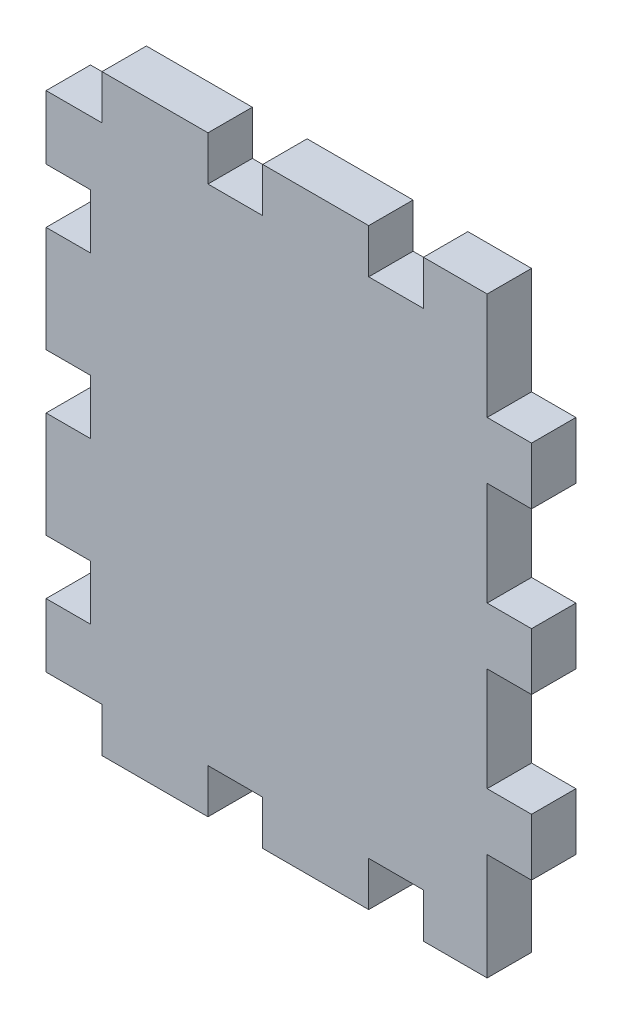
SolidWorks part; units mm, degrees
ref_plane "Front Plane" through (0, 0, 0) normal (0, 0, 1) x (1, 0, 0)
ref_plane "Top Plane" through (0, 0, 0) normal (0, 1, 0) x (1, 0, 0)
ref_plane "Right Plane" through (0, 0, 0) normal (1, 0, 0) x (0, 0, -1)
sketch "Sketch2" plane through (0, 0, 0) normal (0, 0, 1) x (1, 0, 0)
  line L1 (-2, 21.15) -> (-2, 17.975)
  line L2 (-13.5, 21.15) -> (-13.5, 17.975)
  line L3 (-13.5, 17.975) -> (-9.5, 17.975)
  line L4 (-9.5, 21.15) -> (-9.5, 17.975)
  line L5 (13.5, 21.15) -> (13.5, 17.975)
  line L6 (13.5, 17.975) -> (9.5, 17.975)
  line L9 (9.5, 21.15) -> (9.5, 17.975)
  line L10 (-2, 17.975) -> (2, 17.975)
  line L12 (-21.15, 21.15) -> (17.975, 21.15)
  line L13 (-21.15, 21.15) -> (-21.15, -21.15)
  line L14 (-21.15, -21.15) -> (17.975, -21.15)
  line L15 (21.15, 13.5) -> (21.15, 9.5)
  line L16 (-21.15, 21.15) -> (21.15, -21.15) construction
  line L17 (-21.15, -21.15) -> (21.15, 21.15) construction
  line L19 (17.975, 21.15) -> (17.975, 13.5)
  line L20 (21.15, 2) -> (21.15, -2)
  line L21 (21.15, -9.5) -> (21.15, -13.5)
  line L22 (17.975, 9.5) -> (17.975, 2)
  line L23 (17.975, -2) -> (17.975, -9.5)
  line L24 (17.975, -13.5) -> (17.975, -21.15)
  line L30 (2, 21.15) -> (2, 17.975)
  line L31 (-2, 21.15) -> (2, 17.975) construction
  line L32 (-2, 17.975) -> (2, 21.15) construction
  line L33 (-2, 21.15) -> (2, 21.15)
  line L34 (-2, -17.975) -> (-2, -21.15)
  line L35 (-13.5, -17.975) -> (-13.5, -21.15)
  line L36 (-13.5, -21.15) -> (-9.5, -21.15)
  line L37 (-9.5, -17.975) -> (-9.5, -21.15)
  line L38 (13.5, -17.975) -> (13.5, -21.15)
  line L39 (13.5, -21.15) -> (9.5, -21.15)
  line L40 (9.5, -17.975) -> (9.5, -21.15)
  line L41 (-2, -21.15) -> (2, -21.15)
  line L42 (2, -17.975) -> (2, -21.15)
  line L43 (-2, -17.975) -> (2, -21.15) construction
  line L44 (-2, -21.15) -> (2, -17.975) construction
  line L45 (-2, -17.975) -> (2, -17.975)
  line L46 (9.5, -17.975) -> (13.5, -17.975)
  line L47 (-13.5, -17.975) -> (-9.5, -17.975)
  line L49 (-21.15, -2) -> (-17.975, -2)
  line L50 (-21.15, -2) -> (-21.15, 2)
  line L51 (-21.15, 2) -> (-17.975, 2)
  line L52 (-17.975, -2) -> (-17.975, 2)
  line L54 (-21.15, 9.5) -> (-17.975, 9.5)
  line L55 (-21.15, 9.5) -> (-21.15, 13.5)
  line L56 (-21.15, 13.5) -> (-17.975, 13.5)
  line L57 (-17.975, 9.5) -> (-17.975, 13.5)
  line L58 (0, 21.15) -> (0, -21.15) construction
  line L59 (-21.15, -9.5) -> (-17.975, -9.5)
  line L60 (-21.15, -9.5) -> (-21.15, -13.5)
  line L61 (-21.15, -13.5) -> (-17.975, -13.5)
  line L62 (-17.975, -9.5) -> (-17.975, -13.5)
  line L64 (21.15, -13.5) -> (17.975, -13.5)
  line L65 (21.15, -9.5) -> (17.975, -9.5)
  line L67 (21.15, 13.5) -> (17.975, 13.5)
  line L68 (21.15, 9.5) -> (17.975, 9.5)
  line L70 (21.15, 2) -> (17.975, 2)
  line L71 (21.15, -2) -> (17.975, -2)
  point P0 (0, -21.15)
  point P9 (0, 19.5625)
  point P13 (0, 0)
  point P35 (0, 21.15)
  point P46 (0, -19.5625)
  point P62 (-17.975, 0)
  point P63 (-21.15, 0)
  dimension "D4" = 42.3
  dimension "D5" = 42.3
  dimension "D2" = 4
  dimension "D3" = 3.175
  dimension "D6" = 7.5
  dimension "D11" = 7.5
  dimension "D12" = 4
  dimension "D13" = 3.175
  dimension "D14" = 7.5
  dimension "D15" = 7.5
  dimension "D16" = 3.175
  dimension "D17" = 7.5
  dimension "D18" = 7.5
extrude "Boss-Extrude1" add sketch "Sketch2" along normal blind 3.175
sketch "Sketch4" plane through (0, 0, 3.175) normal (0, 0, 1) x (1, 0, 0)
  line L0 (-13.5, 17.975) -> (-13.5, -17.975)
  line L1 (-21.15, 13.5) -> (-17.975, 13.5) construction
  line L2 (-13.5, 13.5) -> (-10.325, 13.5)
  line L3 (-13.5, 13.5) -> (-13.5, 9.5)
  line L4 (-13.5, 9.5) -> (-10.325, 9.5)
  line L5 (-10.325, 13.5) -> (-10.325, 9.5)
  line L6 (-13.5, 2) -> (-10.325, 2)
  line L7 (-13.5, 2) -> (-13.5, -2)
  line L8 (-13.5, -2) -> (-10.325, -2)
  line L9 (-10.325, 2) -> (-10.325, -2)
  line L10 (-13.5, -9.5) -> (-10.325, -9.5)
  line L11 (-13.5, -9.5) -> (-13.5, -13.5)
  line L12 (-13.5, -13.5) -> (-10.325, -13.5)
  line L13 (-10.325, -9.5) -> (-10.325, -13.5)
  line L14 (-17.975, 9.5) -> (-17.975, 13.5) construction
  line L15 (-21.15, 2) -> (-17.975, 2) construction
  line L16 (-21.15, -9.5) -> (-17.975, -9.5) construction
  line L18 (-21.15, 21.15) -> (-13.5, 21.15)
  line L19 (-21.15, 21.15) -> (-21.15, -21.15)
  line L20 (-21.15, -21.15) -> (-13.5, -21.15)
  line L21 (-13.5, 21.15) -> (-13.5, -21.15)
extrude "Cut-Extrude1" cut sketch "Sketch4" against normal blind 10 contours L21 L18 L19 L20 L0 | L5 L2 L0 L4 | L9 L6 L0 L8 | L13 L10 L0 L12
sketch "Sketch3" plane through (0, 0, 3.175) normal (0, 0, 1) x (1, 0, 0)
  line L48 (-13.5406, 18.0156) -> (-13.5406, 13.4594)
  line L49 (-13.5406, 18.0156) -> (-13.5406, 13.4594)
  line L50 (-13.5406, 13.4594) -> (-10.3656, 13.4594)
  line L51 (-13.5406, 13.4594) -> (-10.3656, 13.4594)
  line L52 (-10.3656, 13.4594) -> (-10.3656, 9.5406)
  line L53 (-10.3656, 13.4594) -> (-10.3656, 9.5406)
  line L54 (-10.3656, 9.5406) -> (-13.5406, 9.5406)
  line L55 (-10.3656, 9.5406) -> (-13.5406, 9.5406)
  line L56 (-13.5406, 9.5406) -> (-13.5406, 1.9594)
  line L57 (-13.5406, 9.5406) -> (-13.5406, 1.9594)
  line L58 (-13.5406, 1.9594) -> (-10.3656, 1.9594)
  line L59 (-13.5406, 1.9594) -> (-10.3656, 1.9594)
  line L60 (-10.3656, 1.9594) -> (-10.3656, -1.9594)
  line L61 (-10.3656, 1.9594) -> (-10.3656, -1.9594)
  line L62 (-10.3656, -1.9594) -> (-13.5406, -1.9594)
  line L63 (-10.3656, -1.9594) -> (-13.5406, -1.9594)
  line L64 (-13.5406, -1.9594) -> (-13.5406, -9.5406)
  line L65 (-13.5406, -1.9594) -> (-13.5406, -9.5406)
  line L66 (-13.5406, -9.5406) -> (-10.3656, -9.5406)
  line L67 (-13.5406, -9.5406) -> (-10.3656, -9.5406)
  line L68 (-10.3656, -9.5406) -> (-10.3656, -13.4594)
  line L69 (-10.3656, -9.5406) -> (-10.3656, -13.4594)
  line L70 (-10.3656, -13.4594) -> (-13.5406, -13.4594)
  line L71 (-10.3656, -13.4594) -> (-13.5406, -13.4594)
  line L72 (-13.5406, -13.4594) -> (-13.5406, -18.0156)
  line L73 (-13.5406, -13.4594) -> (-13.5406, -18.0156)
  line L104 (18.0156, -2.0406) -> (21.1906, -2.0406)
  line L105 (21.1906, -2.0406) -> (21.1906, 2.0406)
  line L106 (21.1906, 2.0406) -> (18.0156, 2.0406)
  line L107 (18.0156, 2.0406) -> (18.0156, 9.4594)
  line L108 (18.0156, 9.4594) -> (21.1906, 9.4594)
  line L109 (21.1906, 9.4594) -> (21.1906, 13.5406)
  line L110 (21.1906, 13.5406) -> (18.0156, 13.5406)
  line L111 (18.0156, 13.5406) -> (18.0156, 21.1906)
  line L112 (18.0156, 21.1906) -> (13.4594, 21.1906)
  line L113 (13.4594, 21.1906) -> (13.4594, 18.0156)
  line L114 (13.4594, 18.0156) -> (9.5406, 18.0156)
  line L115 (9.5406, 18.0156) -> (9.5406, 21.1906)
  line L116 (9.5406, 21.1906) -> (1.9594, 21.1906)
  line L117 (1.9594, 21.1906) -> (1.9594, 18.0156)
  line L118 (1.9594, 18.0156) -> (-1.9594, 18.0156)
  line L119 (-1.9594, 18.0156) -> (-1.9594, 21.1906)
  line L120 (-1.9594, 21.1906) -> (-9.5406, 21.1906)
  line L121 (-9.5406, 21.1906) -> (-9.5406, 18.0156)
  line L122 (-9.5406, 18.0156) -> (-13.5406, 18.0156)
  line L140 (-13.5406, -18.0156) -> (-9.5406, -18.0156)
  line L141 (-9.5406, -18.0156) -> (-9.5406, -21.1906)
  line L142 (-9.5406, -21.1906) -> (-1.9594, -21.1906)
  line L143 (-1.9594, -21.1906) -> (-1.9594, -18.0156)
  line L144 (-1.9594, -18.0156) -> (1.9594, -18.0156)
  line L145 (1.9594, -18.0156) -> (1.9594, -21.1906)
  line L146 (1.9594, -21.1906) -> (9.5406, -21.1906)
  line L147 (9.5406, -21.1906) -> (9.5406, -18.0156)
  line L148 (9.5406, -18.0156) -> (13.4594, -18.0156)
  line L149 (13.4594, -18.0156) -> (13.4594, -21.1906)
  line L150 (13.4594, -21.1906) -> (18.0156, -21.1906)
  line L151 (18.0156, -21.1906) -> (18.0156, -13.5406)
  line L152 (18.0156, -13.5406) -> (21.1906, -13.5406)
  line L153 (21.1906, -13.5406) -> (21.1906, -9.4594)
  line L154 (21.1906, -9.4594) -> (18.0156, -9.4594)
  line L155 (18.0156, -9.4594) -> (18.0156, -2.0406)
  line L156 (18.0156, -2.0406) -> (21.1906, -2.0406)
  line L157 (21.1906, -2.0406) -> (21.1906, 2.0406)
  line L158 (21.1906, 2.0406) -> (18.0156, 2.0406)
  line L159 (18.0156, 2.0406) -> (18.0156, 9.4594)
  line L160 (18.0156, 9.4594) -> (21.1906, 9.4594)
  line L161 (21.1906, 9.4594) -> (21.1906, 13.5406)
  line L162 (21.1906, 13.5406) -> (18.0156, 13.5406)
  line L163 (18.0156, 13.5406) -> (18.0156, 21.1906)
  line L164 (18.0156, 21.1906) -> (13.4594, 21.1906)
  line L165 (13.4594, 21.1906) -> (13.4594, 18.0156)
  line L166 (13.4594, 18.0156) -> (9.5406, 18.0156)
  line L167 (9.5406, 18.0156) -> (9.5406, 21.1906)
  line L168 (9.5406, 21.1906) -> (1.9594, 21.1906)
  line L169 (1.9594, 21.1906) -> (1.9594, 18.0156)
  line L170 (1.9594, 18.0156) -> (-1.9594, 18.0156)
  line L171 (-1.9594, 18.0156) -> (-1.9594, 21.1906)
  line L172 (-1.9594, 21.1906) -> (-9.5406, 21.1906)
  line L173 (-9.5406, 21.1906) -> (-9.5406, 18.0156)
  line L174 (-9.5406, 18.0156) -> (-13.5406, 18.0156)
  line L192 (-13.5406, -18.0156) -> (-9.5406, -18.0156)
  line L193 (-9.5406, -18.0156) -> (-9.5406, -21.1906)
  line L194 (-9.5406, -21.1906) -> (-1.9594, -21.1906)
  line L195 (-1.9594, -21.1906) -> (-1.9594, -18.0156)
  line L196 (-1.9594, -18.0156) -> (1.9594, -18.0156)
  line L197 (1.9594, -18.0156) -> (1.9594, -21.1906)
  line L198 (1.9594, -21.1906) -> (9.5406, -21.1906)
  line L199 (9.5406, -21.1906) -> (9.5406, -18.0156)
  line L200 (9.5406, -18.0156) -> (13.4594, -18.0156)
  line L201 (13.4594, -18.0156) -> (13.4594, -21.1906)
  line L202 (13.4594, -21.1906) -> (18.0156, -21.1906)
  line L203 (18.0156, -21.1906) -> (18.0156, -13.5406)
  line L204 (18.0156, -13.5406) -> (21.1906, -13.5406)
  line L205 (21.1906, -13.5406) -> (21.1906, -9.4594)
  line L206 (21.1906, -9.4594) -> (18.0156, -9.4594)
  line L207 (18.0156, -9.4594) -> (18.0156, -2.0406)
  dimension "D1" = 0.0406
extrude "Boss-Extrude2" add sketch "Sketch3" against normal blind 3.175
equation "\"stepper width\"=4.23"
equation "\"stepper hole disctance\"= 3.1"
equation "\"stepper hole diameter\"=0.34"
equation "\"stepper shaft hole\"=2.4"
equation "\"tooth width\"=0.4"
equation "\"tooth thickness\"=0.3175"
equation "\"tooth to side\"=0.75"
equation "\"motor chamber height\"= 6"
equation "\"D4@Sketch2\"=\"stepper width\""
equation "\"D5@Sketch2\"=\"stepper width\""
equation "\"D16@Sketch2\"=\"tooth thickness\""
equation "\"D17@Sketch2\"=\"tooth to side\""
equation "\"D18@Sketch2\"=\"tooth to side\""
